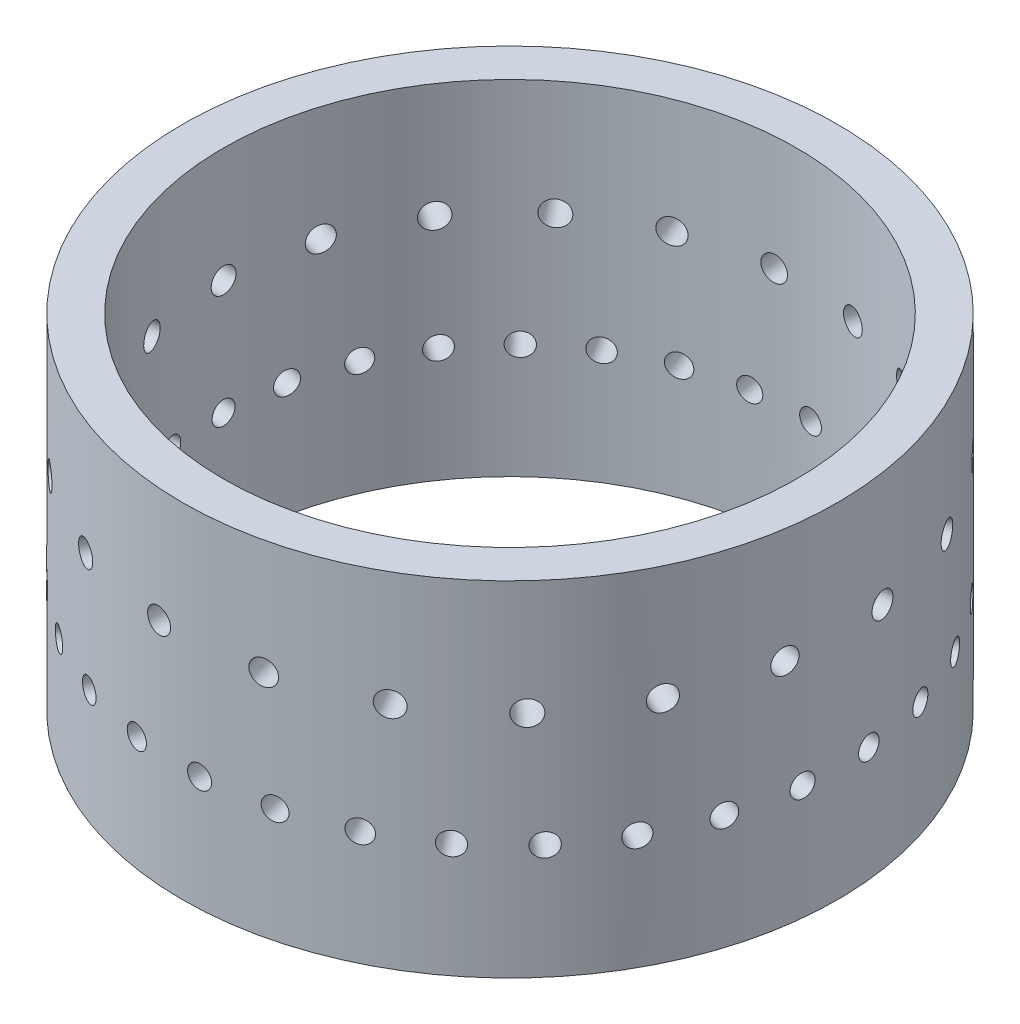
SolidWorks part; units mm, degrees
ref_plane "Front Plane" through (0, 0, 0) normal (0, 0, 1) x (1, 0, 0)
ref_plane "Top Plane" through (0, 0, 0) normal (0, 1, 0) x (1, 0, 0)
ref_plane "Right Plane" through (0, 0, 0) normal (1, 0, 0) x (0, 0, -1)
sketch "Sketch1" plane through (0, 0, 0) normal (0, 1, 0) x (1, 0, 0)
  circle A0 centre (0, 0) radius 22.225
  circle A1 centre (0, 0) radius 25.4
  dimension "D1" = 50.8
  dimension "D2" = 44.45
extrude "Boss-Extrude1" add sketch "Sketch1" along normal blind 26.67
sketch "Sketch2" plane through (0, 0, 0) normal (1, 0, 0) x (0, 0, -1)
  line L0 (-25.4, 0) -> (25.4, 0) construction
  circle A0 centre (0, 8.89) radius 0.889
  dimension "D1" = 1.778
  dimension "D2" = 8.89
extrude "Cut-Extrude1" cut sketch "Sketch2" against normal blind 26.67
sketch "Sketch3" plane through (0, 0, 0) normal (1, 0, 0) x (0, 0, -1)
  line L0 (0, 0) -> (0, 30.9276) construction
pattern_circular "CirPattern1" count 31 over 360 about axis through (0, 0, 0) along (0, 1, 0) of "Cut-Extrude1"
sketch "Sketch4" plane through (0, 0, 0) normal (1, 0, 0) x (0, 0, -1)
  line L0 (0, 0) -> (0, 30.9276) construction
  line L1 (22.225, 26.67) -> (-22.225, 26.67) construction
  circle A0 centre (0, 17.78) radius 0.9652
  dimension "D1" = 1.9304
  dimension "D2" = 8.89
extrude "Cut-Extrude2" cut sketch "Sketch4" against normal blind 26.67
pattern_circular "CirPattern2" count 21 over 360 about axis through (0, 0, 0) along (0, 1, 0) of "Cut-Extrude2"
